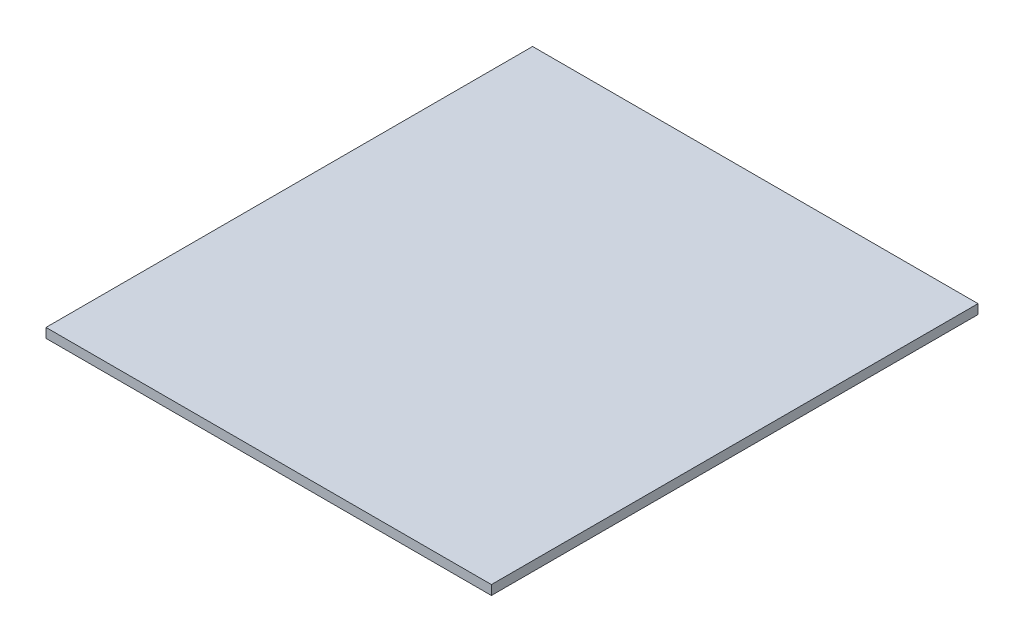
SolidWorks part; units mm, degrees
ref_plane "Front Plane" through (0, 0, 0) normal (0, 0, 1) x (1, 0, 0)
ref_plane "Top Plane" through (0, 0, 0) normal (0, 1, 0) x (1, 0, 0)
ref_plane "Right Plane" through (0, 0, 0) normal (1, 0, 0) x (0, 0, -1)
sketch "Sketch1" plane through (0, 0, 0) normal (0, 1, 0) x (1, 0, 0)
  line L1 (0, 0) -> (139.5, 0)
  line L2 (0, 0) -> (0, 152.4)
  line L3 (0, 152.4) -> (139.5, 152.4)
  line L4 (139.5, 0) -> (139.5, 152.4)
  dimension "D1" = 152.4
  dimension "D2" = 139.5
extrude "Boss-Extrude1" add sketch "Sketch1" along normal blind 6.35
sketch "Sketch2" plane through (0, 6.35, 0) normal (0, 1, 0) x (1, 0, 0)
  line L0 (0, 0) -> (139.5, 0) construction
  line L1 (0, 152.4) -> (139.5, 152.4)
  line L2 (0, 152.4) -> (0, 0)
  line L3 (0, 0) -> (139.5, 0)
  line L4 (139.5, 152.4) -> (139.5, 0)
  line L5 (139.5, 0) -> (139.5, 152.4) construction
extrude "Cut-Extrude1" cut sketch "Sketch2" against normal blind 3.375
